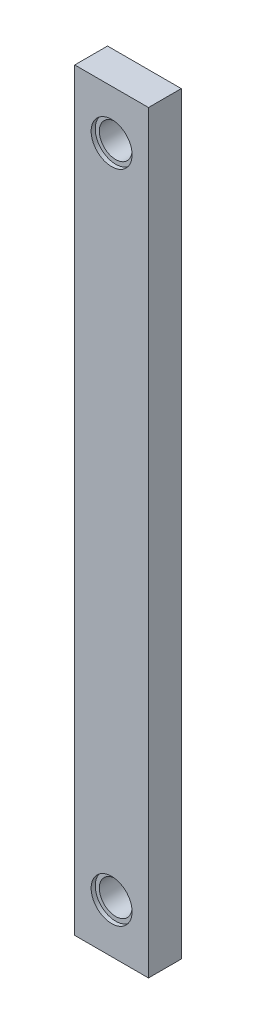
SolidWorks part; units mm, degrees
ref_plane "Front Plane" through (0, 0, 0) normal (0, 0, 1) x (1, 0, 0)
ref_plane "Top Plane" through (0, 0, 0) normal (0, 1, 0) x (1, 0, 0)
ref_plane "Right Plane" through (0, 0, 0) normal (1, 0, 0) x (0, 0, -1)
sketch "Sketch1" plane through (0, 0, 0) normal (0, 0, 1) x (1, 0, 0)
  line L0 (0, 0) -> (0, 254) construction
  circle A2 centre (0, 0) radius 6.35
  circle A3 centre (0, 0) radius 7.9375
  dimension "D2" = 12.7
  dimension "D3" = 15.875
  dimension "D1" = 254
sketch "Sketch2" plane through (0, 0, 0) normal (0, 0, 1) x (1, 0, 0)
  line L0 (0, 0) -> (0, 254) construction
  line L3 (-14.2875, 273.05) -> (14.2875, 273.05)
  line L4 (-14.2875, 273.05) -> (-14.2875, -19.05)
  line L5 (-14.2875, -19.05) -> (14.2875, -19.05)
  line L6 (14.2875, 273.05) -> (14.2875, -19.05)
  line L7 (-14.2875, 273.05) -> (14.2875, -19.05) construction
  line L8 (-14.2875, -19.05) -> (14.2875, 273.05) construction
  line L9 (0, 0) -> (0, -19.05) construction
  line L10 (0, 254) -> (0, 273.05) construction
  circle A2 centre (0, 0) radius 7.9375 construction
  point P6 (0, 127)
  dimension "D2" = 6.35
  dimension "D1" = 19.05
extrude "Boss-Extrude1" add sketch "Sketch2" along normal mid plane 12.7
sketch "Sketch4" plane through (0, 0, 0) normal (0, 0, 1) x (1, 0, 0)
  circle A0 centre (0, 0) radius 6.35 construction
  circle A1 centre (0, 0) radius 6.35
extrude "Cut-Extrude1" cut sketch "Sketch4" against normal through all both and the other way through all
sketch "Sketch5" plane through (0, 0, 6.35) normal (0, 0, 1) x (1, 0, 0)
  circle A0 centre (0, 0) radius 7.9375 construction
  circle A1 centre (0, 0) radius 7.9375
extrude "Cut-Extrude2" cut sketch "Sketch5" against normal blind 1.5875
ref_plane "Plane1" through (0, 127, 0) normal (0, -1, 0) x (-1, 0, 0)
mirror "Mirror1" about plane through (0, 127, 0) normal (0, -1, 0) of "Cut-Extrude1", "Cut-Extrude2"
sketch "Sketch6" [suppressed] plane through (0, 0, 0) normal (0, 0, 1) x (1, 0, 0)
  line L1 (0, 0) -> (0, 254) construction
  point P0 (0, 50.8)
  dimension "D1" = 50.8
pattern_sketch "Sketch-Pattern1" [suppressed]
equation "\"shank_lower_len\"= 8"
equation "\"shank_lever_len\"=2"
equation "\"D1@Sketch1\"     = \"shank_upper_len\""
equation "\"shank_upper_len\"= 10"
equation "\"D1@Sketch6\"=\"shank_lever_len\""
